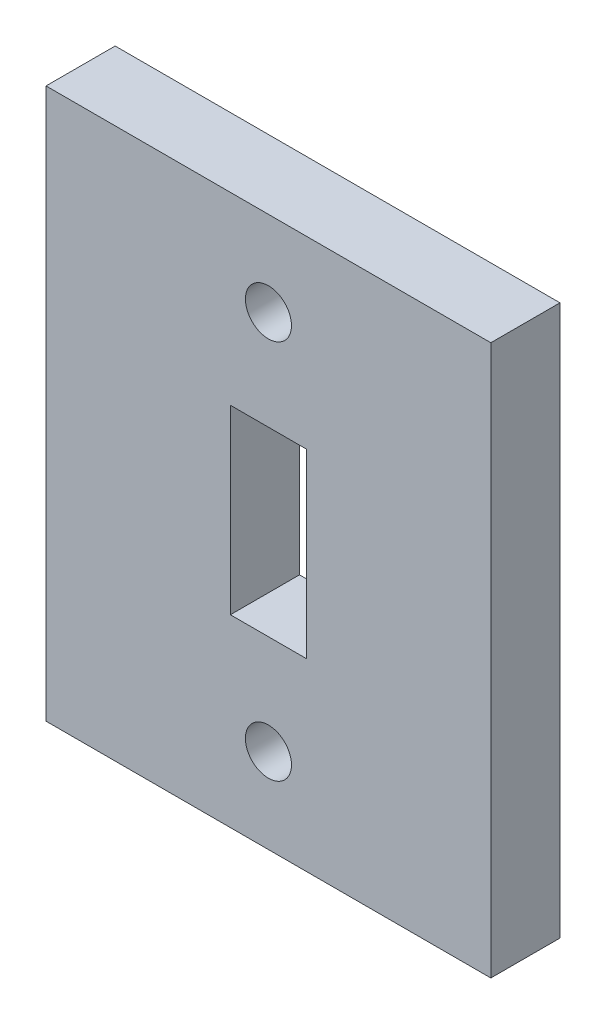
SolidWorks part; units mm, degrees
ref_plane "Front Plane" through (0, 0, 0) normal (0, 0, 1) x (1, 0, 0)
ref_plane "Top Plane" through (0, 0, 0) normal (0, 1, 0) x (1, 0, 0)
ref_plane "Right Plane" through (0, 0, 0) normal (1, 0, 0) x (0, 0, -1)
sketch "Sketch1" plane through (0, 0, 0) normal (0, 0, 1) x (1, 0, 0)
  line L0 (0, 23.874) -> (19.302, 23.874)
  line L1 (19.302, 23.874) -> (19.302, 0)
  line L2 (0, 0) -> (19.302, 0)
  line L3 (0, 23.874) -> (0, 0)
  line L5 (8, 15.874) -> (11.302, 15.874)
  line L6 (8, 15.874) -> (8, 8)
  line L7 (8, 8) -> (11.302, 8)
  line L8 (11.302, 15.874) -> (11.302, 8)
  dimension "D1" = 7.874
  dimension "D2" = 3.302
  dimension "D3" = 8
extrude "Boss-Extrude1" add sketch "Sketch1" along normal blind 3
sketch "Sketch3" plane through (0, 0, 0) normal (0, 0, -1) x (-1, 0, 0)
  line L0 (-9.651, 20.192) -> (-9.651, 15.874) construction
  line L1 (-11.302, 15.874) -> (-8, 15.874) construction
  line L2 (-8, 11.937) -> (0, 11.937) construction
  line L3 (-8, 15.874) -> (-8, 8) construction
  line L4 (0, 23.874) -> (0, 0) construction
  circle A0 centre (-9.651, 20.192) radius 1
  circle A1 centre (-9.651, 3.682) radius 1
  dimension "D1" = 2
  dimension "D2" = 4.318
extrude "Cut-Extrude1" cut sketch "Sketch3" against normal through all
equation "\"depth\"= 7.3"
equation "\"height\"= 9.5"
equation "\"width\"= 8.60"
equation "\"flipWidth\"= 6.5"
equation "\"flipHeight\"= 4"
equation "\"spindleLength\"= 7.75"
equation "\"bearingID\"= 0.1559"
equation "\"bearingOD\"= 0.3539\t"
equation "\"motorWidth\"= 0.79"
equation "\"motorHeight\"= 1.0"
equation "\"motorLength\"= 1.58"
equation "\"spindleMaxDiam\"= 2.75"
equation "\"totalLength\"= 15"
equation "\"stopperWidth\"= 0.13"
equation "\"stopperHeight\"= 0.31"
equation "\"stopperLength\"= 8.73"
equation "\"D1@Sketch1\"=\"stopperHeight\""
equation "\"D2@Sketch1\"=\"stopperWidth\""
equation "\"stopperLengthFromTop\"= 1.2 + 0.2"
equation "\"stopperHolesDistance\"= 0.17"
equation "\"D2@Sketch3\"=\"stopperHolesDistance\""
